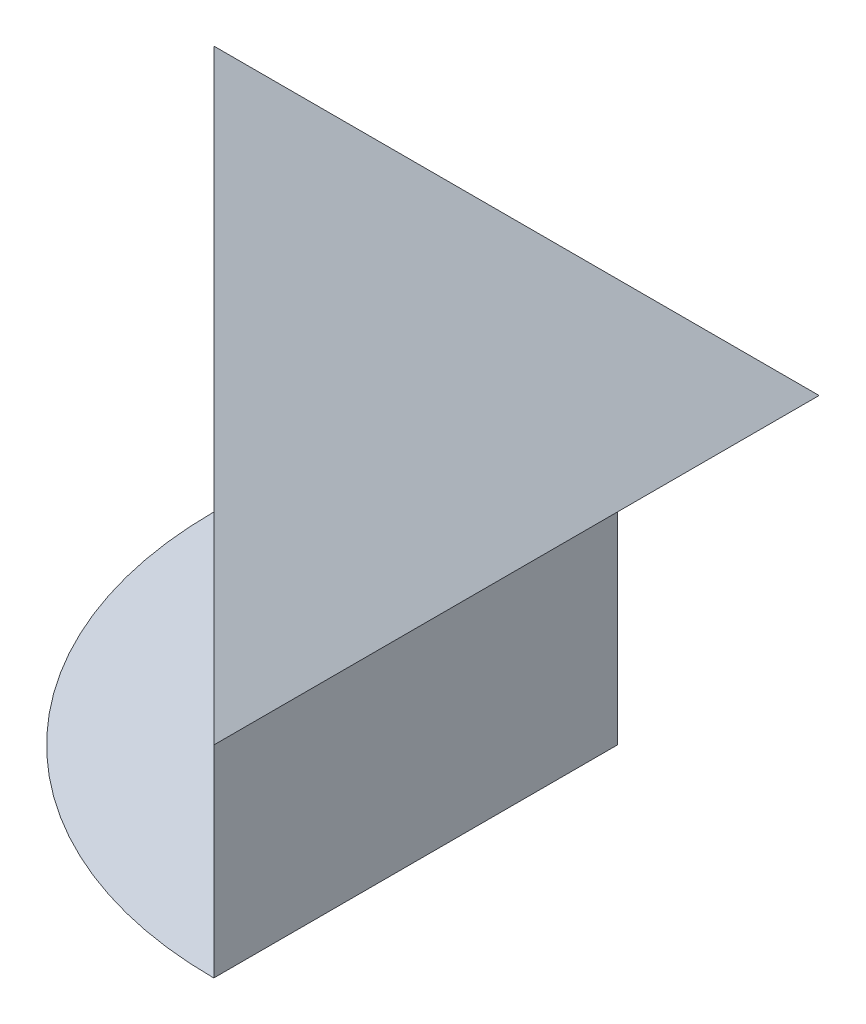
SolidWorks part; units mm, degrees
ref_plane "Front Plane" through (0, 0, 0) normal (0, 0, 1) x (1, 0, 0)
ref_plane "Top Plane" through (0, 0, 0) normal (0, 1, 0) x (1, 0, 0)
ref_plane "Right Plane" through (0, 0, 0) normal (1, 0, 0) x (0, 0, -1)
sketch "Sketch1" plane through (0, 0, 0) normal (0, 0, 1) x (1, 0, 0)
  line L0 (0, 30) -> (-10, 30)
  line L1 (0, 0) -> (40, 0)
  line L2 (0, 0) -> (0, 30)
  line L3 (0, 30) -> (40, 30)
  line L4 (40, 0) -> (40, 30)
  line L5 (40, 30) -> (50, 30)
  line L6 (50, 30) -> (20, 60)
  line L7 (20, 60) -> (-10, 30)
  dimension "D1" = 40
  dimension "D2" = 30
  dimension "D3" = 10
  dimension "D4" = 10
  dimension "D5" = 30
  dimension "D6" = 30
extrude "Boss-Extrude2" add sketch "Sketch1" along normal blind 60 contours L6 L7 L0 L3 L5 | L1 L4 L3 L2
sketch "Sketch3" plane through (0, 0, 0) normal (1, 0, 0) x (0, 0, -1)
  line L0 (-60, 0) -> (0, 0) construction
  line L1 (-50, 0) -> (-10, 0)
  line L2 (-50, 0) -> (-50, 30)
  line L3 (-50, 30) -> (-10, 30)
  line L4 (-10, 0) -> (-10, 30)
  line L5 (-10, 30) -> (0, 30)
  line L6 (0, 30) -> (-30, 60)
  line L7 (-30, 60) -> (-60, 30)
  line L8 (-60, 30) -> (-50, 30)
  line L9 (0, 30) -> (-10, 30)
  line L10 (-10, 30) -> (-10, 0)
  line L11 (-10, 0) -> (0, 0)
  line L12 (0, 0) -> (0, 30)
  line L13 (0, 30) -> (0, 60)
  line L14 (-30, 60) -> (0, 60)
  line L15 (-30, 60) -> (-60, 60)
  line L16 (-60, 30) -> (-60, 60)
  line L18 (-50, 30) -> (-60, 30)
  line L19 (-50, 30) -> (-50, 0)
  line L20 (-50, 0) -> (-60, 0)
  line L21 (-60, 30) -> (-60, 0)
  dimension "D1" = 10
  dimension "D2" = 10
  dimension "D3" = 30
  dimension "D4" = 10
  dimension "D5" = 10
  dimension "D6" = 30
  dimension "D7" = 30
  dimension "D8" = 30
extrude "Cut-Extrude1" cut sketch "Sketch3" along normal blind 60 contours L14 L6 L13 | L16 L7 L15 | L11 L12 L5 L4 | L18 L21 L20 L19
sketch "Sketch4" plane through (0, 0, 0) normal (1, 0, 0) x (0, 0, -1)
  line L0 (-60, 30) -> (-50, 40)
  line L1 (-50, 40) -> (-60, 40)
  line L2 (-60, 40) -> (-60, 30)
extrude "Cut-Extrude2" cut sketch "Sketch4" against normal blind 60
sketch "Sketch5" plane through (0, 0, 0) normal (1, 0, 0) x (0, 0, -1)
  line L0 (-10, 40) -> (0, 40)
  line L1 (0, 40) -> (0, 30)
  line L2 (0, 30) -> (-10, 40)
extrude "Cut-Extrude3" cut sketch "Sketch5" against normal blind 60
ref_plane "Plane1" through (0, 60, 0) normal (0, 1, 0) x (1, 0, 0)
sketch "Sketch6" plane through (0, 60, 0) normal (0, 1, 0) x (1, 0, 0)
  line L0 (50, 0) -> (-10, 0)
  line L1 (50, 0) -> (50, -60)
  line L2 (50, -60) -> (-10, 0)
  line L3 (-10, 0) -> (-10, -60)
  line L4 (-10, -60) -> (50, -60)
extrude "Cut-Extrude4" cut sketch "Sketch6" against normal blind 60 contours L3 L4 L2
sketch "Sketch7" plane through (0, 0, 0) normal (0, -1, 0) x (1, 0, 0)
  line L0 (40, 50) -> (0, 10) construction
  line L1 (40, 10) -> (0, 10) construction
  line L2 (0, 10) -> (40, 10)
  line L3 (40, 10) -> (40, 50)
  arc A0 (40, 50) -> (0, 10) centre (40, 10) ccw
  dimension "D1" = 40
extrude "Boss-Extrude7" add sketch "Sketch7" against normal blind 0.0001
